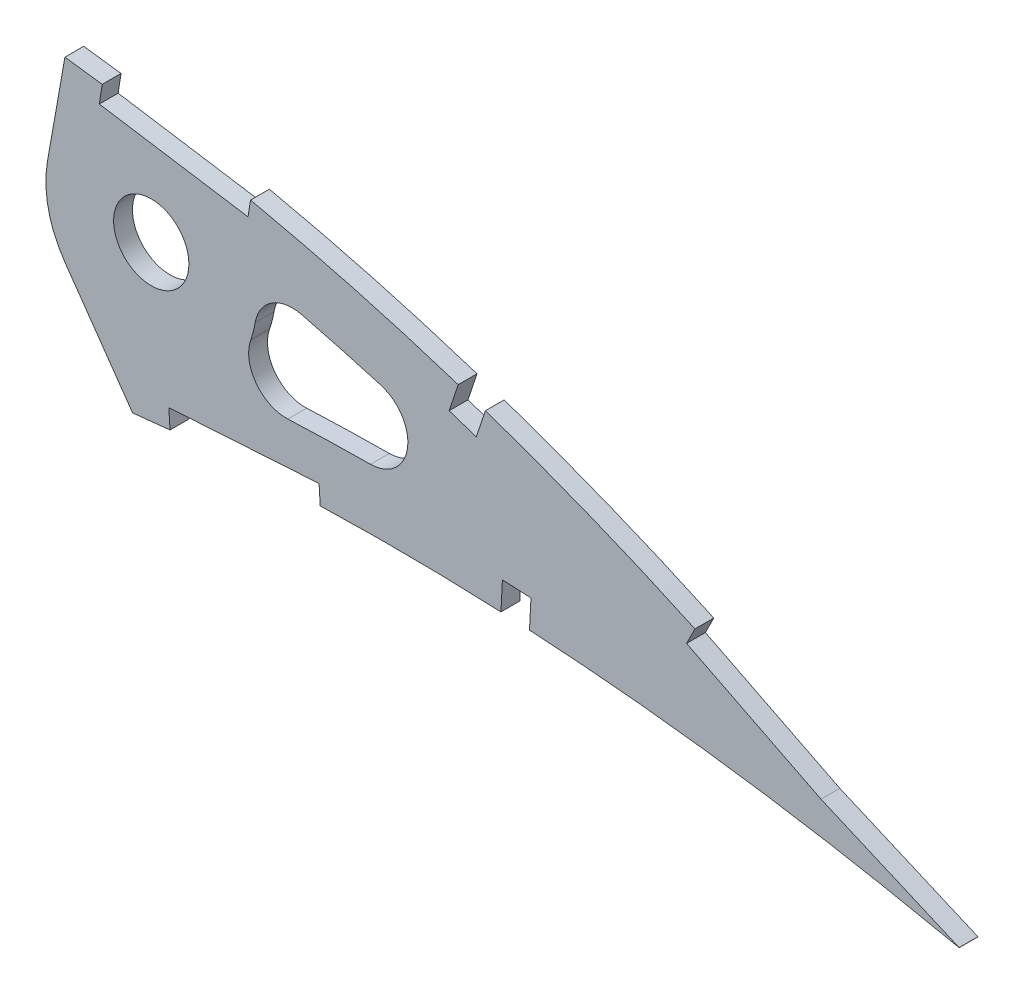
SolidWorks part; units mm, degrees
material "Plywood"
ref_plane "Front Plane" through (0, 0, 0) normal (0, 0, 1) x (1, 0, 0)
ref_plane "Top Plane" through (0, 0, 0) normal (0, 1, 0) x (1, 0, 0)
ref_plane "Right Plane" through (0, 0, 0) normal (1, 0, 0) x (0, 0, -1)
curve "Curve1"
  spline degree 3 poles (0, 0, 0) (0.1249, -0.5894, 0) (0.3751, -1.7709, 0) (1.0551, -3.4717, 0) (1.9543, -5.1067, 0) (3.0917, -6.6716, 0) (4.4597, -8.1658, 0) (6.0551, -9.5909, 0) (7.8766, -10.9463, 0) (9.9217, -12.2312, 0) (12.1874, -13.447, 0) (14.6712, -14.593, 0) (17.3708, -15.6688, 0) (20.2833, -16.6729, 0) (23.4051, -17.607, 0) (26.7332, -18.4687, 0) (30.2639, -19.2592, 0) (33.9938, -19.9766, 0) (37.9188, -20.6214, 0) (42.0348, -21.1935, 0) (46.3376, -21.6931, 0) (50.823, -22.1192, 0) (55.4866, -22.4726, 0) (60.3236, -22.7538, 0) (65.3294, -22.9634, 0) (70.4993, -23.1008, 0) (75.828, -23.1681, 0) (81.3109, -23.1662, 0) (86.9426, -23.0948, 0) (92.7182, -22.9577, 0) (98.6323, -22.754, 0) (104.6794, -22.4863, 0) (110.8541, -22.1572, 0) (117.1509, -21.7679, 0) (123.5642, -21.32, 0) (130.0885, -20.8172, 0) (136.7178, -20.2607, 0) (143.4464, -19.6538, 0) (150.2683, -18.9994, 0) (157.1776, -18.2998, 0) (164.1682, -17.5581, 0) (171.2339, -16.7767, 0) (178.3687, -15.9599, 0) (185.566, -15.1091, 0) (192.8198, -14.2292, 0) (200.1233, -13.3218, 0) (207.4703, -12.3905, 0) (214.8542, -11.4396, 0) (222.2681, -10.469, 0) (229.7058, -9.4856, 0) (237.1601, -8.4887, 0) (244.6246, -7.4833, 0) (252.0922, -6.4726, 0) (259.5558, -5.4569, 0) (267.0088, -4.4404, 0) (274.4442, -3.4259, 0) (281.8548, -2.4135, 0) (289.2339, -1.4081, 0) (296.574, -0.4098, 0) (303.8684, 0.5795, 0) (311.1101, 1.5569, 0) (318.2922, 2.521, 0) (325.4074, 3.4714, 0) (332.4485, 4.4082, 0) (339.3029, 5.3032, 0) (345.9529, 6.204, 0) (352.4207, 6.9424, 0) (358.808, 7.5727, 0) (365.1214, 8.0894, 0) (371.3533, 8.5001, 0) (377.4966, 8.8075, 0) (383.544, 9.0161, 0) (389.4878, 9.132, 0) (395.3205, 9.1582, 0) (401.0343, 9.1029, 0) (406.6218, 8.9708, 0) (412.075, 8.7675, 0) (417.3864, 8.5002, 0) (422.5485, 8.1759, 0) (427.5535, 7.7996, 0) (432.3944, 7.38, 0) (437.0637, 6.9232, 0) (441.5544, 6.4344, 0) (445.8598, 5.924, 0) (449.973, 5.3952, 0) (453.8879, 4.8568, 0) (457.5982, 4.3142, 0) (461.0979, 3.7743, 0) (464.3817, 3.2423, 0) (467.4441, 2.7253, 0) (470.2803, 2.228, 0) (472.8856, 1.7553, 0) (475.2562, 1.3133, 0) (477.3874, 0.904, 0) (479.2765, 0.5343, 0) (480.9199, 0.2058, 0) (482.3151, -0.077, 0) (483.4599, -0.3128, 0) (484.3523, -0.4979, 0) (484.9907, -0.6325, 0) (485.3743, -0.7125, 0) (485.5448, -0.7489, 0) (485.5874, -0.758, 0) knots 0 0 0 0 0.003638 0.007293 0.011028 0.014901 0.018963 0.023258 0.027821 0.032679 0.037853 0.043362 0.049215 0.055422 0.061989 0.068918 0.076211 0.083868 0.091887 0.100266 0.109 0.118085 0.127515 0.137285 0.147388 0.157816 0.168563 0.179619 0.190977 0.202627 0.21456 0.226767 0.239236 0.251959 0.264924 0.27812 0.291536 0.30516 0.318981 0.332985 0.347163 0.361499 0.375981 0.390597 0.405333 0.420175 0.43511 0.450124 0.465203 0.480333 0.495501 0.51069 0.525887 0.541078 0.556247 0.571382 0.586466 0.601485 0.616424 0.631269 0.646007 0.660621 0.675098 0.689423 0.703582 0.716908 0.730009 0.742952 0.755726 0.76832 0.780724 0.792927 0.804916 0.816679 0.828204 0.839475 0.850481 0.861208 0.871639 0.881763 0.891564 0.901027 0.910139 0.918884 0.927249 0.935221 0.942785 0.949928 0.956638 0.962904 0.968712 0.974054 0.978918 0.983297 0.98718 0.990561 0.993433 0.995791 0.99763 0.998946 0.999737 1 1 1 1
curve "Curve2"
  spline degree 3 poles (486.1938, 0.758, 0) (486.1565, 0.781, 0) (486.0077, 0.8729, 0) (485.6723, 1.0786, 0) (485.1139, 1.4213, 0) (484.3321, 1.8984, 0) (483.3276, 2.5088, 0) (482.0999, 3.2482, 0) (480.6498, 4.1141, 0) (478.9775, 5.1026, 0) (477.0833, 6.2089, 0) (474.9678, 7.4286, 0) (472.6313, 8.7548, 0) (470.0748, 10.182, 0) (467.2989, 11.7035, 0) (464.3043, 13.3123, 0) (461.0921, 15.0004, 0) (457.6635, 16.7605, 0) (454.019, 18.5827, 0) (450.1605, 20.4596, 0) (446.0892, 22.3819, 0) (441.8065, 24.3391, 0) (437.3149, 26.3234, 0) (432.6155, 28.3224, 0) (427.7112, 30.3274, 0) (422.6039, 32.3272, 0) (417.2967, 34.3124, 0) (411.7916, 36.2703, 0) (406.0928, 38.1924, 0) (400.203, 40.0661, 0) (394.1264, 41.8812, 0) (387.8666, 43.626, 0) (381.4288, 45.2916, 0) (374.8171, 46.8658, 0) (368.037, 48.3381, 0) (361.0939, 49.6996, 0) (353.9938, 50.9366, 0) (346.7562, 52.0484, 0) (339.4976, 52.9732, 0) (332.2539, 53.8802, 0) (325.021, 54.7322, 0) (317.6998, 55.5482, 0) (310.2971, 56.3235, 0) (302.8205, 57.0556, 0) (295.2774, 57.7415, 0) (287.6757, 58.3791, 0) (280.0227, 58.9648, 0) (272.3266, 59.4977, 0) (264.5949, 59.9731, 0) (256.8359, 60.3907, 0) (249.0573, 60.7475, 0) (241.2675, 61.0411, 0) (233.4745, 61.2698, 0) (225.6865, 61.4312, 0) (217.912, 61.5245, 0) (210.159, 61.547, 0) (202.4359, 61.4984, 0) (194.7508, 61.377, 0) (187.1122, 61.1811, 0) (179.5282, 60.9103, 0) (172.0069, 60.5649, 0) (164.5567, 60.1418, 0) (157.1855, 59.6438, 0) (149.9016, 59.0688, 0) (142.713, 58.4167, 0) (135.6273, 57.6901, 0) (128.6522, 56.887, 0) (121.7954, 56.0099, 0) (115.0642, 55.0603, 0) (108.4663, 54.0378, 0) (102.0087, 52.9453, 0) (95.6983, 51.784, 0) (89.542, 50.5572, 0) (83.5463, 49.2652, 0) (77.7176, 47.912, 0) (72.062, 46.4999, 0) (66.5855, 45.0315, 0) (61.2937, 43.5103, 0) (56.192, 41.9397, 0) (51.2862, 40.3215, 0) (46.5802, 38.6618, 0) (42.0796, 36.9619, 0) (37.788, 35.2268, 0) (33.7103, 33.4591, 0) (29.8497, 31.6641, 0) (26.2104, 29.8437, 0) (22.7951, 28.0033, 0) (19.6072, 26.1454, 0) (16.6497, 24.2737, 0) (13.924, 22.3929, 0) (11.4337, 20.504, 0) (9.1798, 18.612, 0) (7.1636, 16.7197, 0) (5.388, 14.8284, 0) (3.8531, 12.9414, 0) (2.5606, 11.0602, 0) (1.511, 9.1866, 0) (0.7066, 7.3219, 0) (0.1466, 5.4673, 0) (-0.16, 3.6254, 0) (-0.2363, 1.7948, 0) (-0.0786, 0.5974, 0) (0, 0, 0) knots 0 0 0 0 0.000254 0.001015 0.002283 0.004057 0.006331 0.009105 0.012374 0.016134 0.02038 0.025106 0.030306 0.035972 0.0421 0.048678 0.055702 0.06316 0.071046 0.07935 0.088063 0.097176 0.106678 0.116562 0.126814 0.137428 0.148394 0.1597 0.171338 0.183298 0.19557 0.208144 0.221012 0.234162 0.247587 0.261277 0.275223 0.289414 0.303771 0.317689 0.331784 0.34604 0.360444 0.374983 0.38964 0.404403 0.419257 0.434187 0.449177 0.464215 0.479284 0.49437 0.509458 0.524532 0.539579 0.554583 0.56953 0.584403 0.599191 0.613877 0.628447 0.642889 0.657186 0.671326 0.685294 0.699078 0.712665 0.726043 0.739198 0.752118 0.764792 0.777208 0.789356 0.801224 0.812804 0.824083 0.835055 0.84571 0.856038 0.866034 0.875689 0.884998 0.893953 0.902553 0.910789 0.918661 0.926166 0.933303 0.940071 0.946475 0.952518 0.958205 0.963547 0.968557 0.97325 0.977651 0.981787 0.985694 0.989415 0.993001 0.996508 1 1 1 1
sketch "Sketch1" plane through (0, 0, 0) normal (0, 0, 1) x (1, 0, 0)
  line L10 (485.5874, -0.758) -> (490.1477, -1.6846)
  line L24 (486.1938, 0.758) -> (490.1477, -1.6846)
  spline S2 degree 3 poles (-3866.8103, -1018.8258) (79.7559, 75.3438) (-9.1933, 22.1629) (1.0551, -3.4717) (1.9543, -5.1067) (3.0917, -6.6716) (4.4597, -8.1658) (6.0551, -9.5909) (7.8766, -10.9463) (9.9217, -12.2312) (12.1874, -13.447) (14.6712, -14.593) (17.3708, -15.6688) (20.2833, -16.6729) (23.4051, -17.607) (26.7332, -18.4687) (30.2639, -19.2592) (33.9938, -19.9766) (37.9188, -20.6214) (42.0348, -21.1935) (46.3376, -21.6931) (50.823, -22.1192) (55.4866, -22.4726) (60.3236, -22.7538) (65.3294, -22.9634) (70.4993, -23.1008) (75.828, -23.1681) (81.3109, -23.1662) (86.9426, -23.0948) (92.7182, -22.9577) (98.6323, -22.754) (104.6794, -22.4863) (110.8541, -22.1572) (117.1509, -21.7679) (123.5642, -21.32) (130.0885, -20.8172) (136.7178, -20.2607) (143.4464, -19.6538) (150.2683, -18.9994) (157.1776, -18.2998) (164.1682, -17.5581) (171.2339, -16.7767) (178.3687, -15.9599) (185.566, -15.1091) (192.8198, -14.2292) (200.1233, -13.3218) (207.4703, -12.3905) (214.8542, -11.4396) (222.2681, -10.469) (229.7058, -9.4856) (237.1601, -8.4887) (244.6246, -7.4833) (252.0922, -6.4726) (259.5558, -5.4569) (267.0088, -4.4404) (274.4442, -3.4259) (281.8548, -2.4135) (289.2339, -1.4081) (296.574, -0.4098) (303.8684, 0.5795) (311.1101, 1.5569) (318.2922, 2.521) (325.4074, 3.4714) (332.4485, 4.4082) (339.3029, 5.3032) (345.9529, 6.204) (352.4207, 6.9424) (358.808, 7.5727) (365.1214, 8.0894) (371.3533, 8.5001) (377.4966, 8.8075) (383.544, 9.0161) (389.4878, 9.132) (395.3205, 9.1582) (401.0343, 9.1029) (406.6218, 8.9708) (412.075, 8.7675) (417.3864, 8.5002) (422.5485, 8.1759) (427.5535, 7.7996) (432.3944, 7.38) (437.0637, 6.9232) (441.5544, 6.4344) (445.8598, 5.924) (449.973, 5.3952) (453.8879, 4.8568) (457.5982, 4.3142) (461.0979, 3.7743) (464.3817, 3.2423) (467.4441, 2.7253) (470.2803, 2.228) (472.8856, 1.7553) (475.2562, 1.3133) (477.3874, 0.904) (479.2765, 0.5343) (480.9199, 0.2058) (482.3151, -0.077) (483.4599, -0.3128) (484.3523, -0.4979) (484.9907, -0.6325) (504.0158, -4.6034) (520.901, -17.6411) (1368.8084, 3899.3631) knots -0.155184 -0.155184 -0.155184 -0.155184 0.003638 0.007293 0.011028 0.014901 0.018963 0.023258 0.027821 0.032679 0.037853 0.043362 0.049215 0.055422 0.061989 0.068918 0.076211 0.083868 0.091887 0.100266 0.109 0.118085 0.127515 0.137285 0.147388 0.157816 0.168563 0.179619 0.190977 0.202627 0.21456 0.226767 0.239236 0.251959 0.264924 0.27812 0.291536 0.30516 0.318981 0.332985 0.347163 0.361499 0.375981 0.390597 0.405333 0.420175 0.43511 0.450124 0.465203 0.480333 0.495501 0.51069 0.525887 0.541078 0.556247 0.571382 0.586466 0.601485 0.616424 0.631269 0.646007 0.660621 0.675098 0.689423 0.703582 0.716908 0.730009 0.742952 0.755726 0.76832 0.780724 0.792927 0.804916 0.816679 0.828204 0.839475 0.850481 0.861208 0.871639 0.881763 0.891564 0.901027 0.910139 0.918884 0.927249 0.935221 0.942785 0.949928 0.956638 0.962904 0.968712 0.974054 0.978918 0.983297 0.98718 0.990561 0.993433 0.995791 0.99763 0.998946 0.999737 1.115177 1.115177 1.115177 1.115177 only from (0, 0) to (485.5874, -0.758) construction
  spline S3 degree 3 poles (2637.6242, 3371.1949) (518.0891, -28.6046) (504.1645, -10.2642) (485.6723, 1.0786) (485.1139, 1.4213) (484.3321, 1.8984) (483.3276, 2.5088) (482.0999, 3.2482) (480.6498, 4.1141) (478.9775, 5.1026) (477.0833, 6.2089) (474.9678, 7.4286) (472.6313, 8.7548) (470.0748, 10.182) (467.2989, 11.7035) (464.3043, 13.3123) (461.0921, 15.0004) (457.6635, 16.7605) (454.019, 18.5827) (450.1605, 20.4596) (446.0892, 22.3819) (441.8065, 24.3391) (437.3149, 26.3234) (432.6155, 28.3224) (427.7112, 30.3274) (422.6039, 32.3272) (417.2967, 34.3124) (411.7916, 36.2703) (406.0928, 38.1924) (400.203, 40.0661) (394.1264, 41.8812) (387.8666, 43.626) (381.4288, 45.2916) (374.8171, 46.8658) (368.037, 48.3381) (361.0939, 49.6996) (353.9938, 50.9366) (346.7562, 52.0484) (339.4976, 52.9732) (332.2539, 53.8802) (325.021, 54.7322) (317.6998, 55.5482) (310.2971, 56.3235) (302.8205, 57.0556) (295.2774, 57.7415) (287.6757, 58.3791) (280.0227, 58.9648) (272.3266, 59.4977) (264.5949, 59.9731) (256.8359, 60.3907) (249.0573, 60.7475) (241.2675, 61.0411) (233.4745, 61.2698) (225.6865, 61.4312) (217.912, 61.5245) (210.159, 61.547) (202.4359, 61.4984) (194.7508, 61.377) (187.1122, 61.1811) (179.5282, 60.9103) (172.0069, 60.5649) (164.5567, 60.1418) (157.1855, 59.6438) (149.9016, 59.0688) (142.713, 58.4167) (135.6273, 57.6901) (128.6522, 56.887) (121.7954, 56.0099) (115.0642, 55.0603) (108.4663, 54.0378) (102.0087, 52.9453) (95.6983, 51.784) (89.542, 50.5572) (83.5463, 49.2652) (77.7176, 47.912) (72.062, 46.4999) (66.5855, 45.0315) (61.2937, 43.5103) (56.192, 41.9397) (51.2862, 40.3215) (46.5802, 38.6618) (42.0796, 36.9619) (37.788, 35.2268) (33.7103, 33.4591) (29.8497, 31.6641) (26.2104, 29.8437) (22.7951, 28.0033) (19.6072, 26.1454) (16.6497, 24.2737) (13.924, 22.3929) (11.4337, 20.504) (9.1798, 18.612) (7.1636, 16.7197) (5.388, 14.8284) (3.8531, 12.9414) (2.5606, 11.0602) (1.511, 9.1866) (0.7066, 7.3219) (0.1466, 5.4673) (-0.16, 3.6254) (-1.3078, -23.9112) (100.477, -44.4073) (-3985.5392, -325.5751) knots -0.123624 -0.123624 -0.123624 -0.123624 0.000254 0.001015 0.002283 0.004057 0.006331 0.009105 0.012374 0.016134 0.02038 0.025106 0.030306 0.035972 0.0421 0.048678 0.055702 0.06316 0.071046 0.07935 0.088063 0.097176 0.106678 0.116562 0.126814 0.137428 0.148394 0.1597 0.171338 0.183298 0.19557 0.208144 0.221012 0.234162 0.247587 0.261277 0.275223 0.289414 0.303771 0.317689 0.331784 0.34604 0.360444 0.374983 0.38964 0.404403 0.419257 0.434187 0.449177 0.464215 0.479284 0.49437 0.509458 0.524532 0.539579 0.554583 0.56953 0.584403 0.599191 0.613877 0.628447 0.642889 0.657186 0.671326 0.685294 0.699078 0.712665 0.726043 0.739198 0.752118 0.764792 0.777208 0.789356 0.801224 0.812804 0.824083 0.835055 0.84571 0.856038 0.866034 0.875689 0.884998 0.893953 0.902553 0.910789 0.918661 0.926166 0.933303 0.940071 0.946475 0.952518 0.958205 0.963547 0.968557 0.97325 0.977651 0.981787 0.985694 0.989415 0.993001 0.996508 1.148636 1.148636 1.148636 1.148636 only from (486.1938, 0.758) to (0, 0) construction
  spline S4 degree 3 poles (0, 0) (0.1249, -0.5894) (0.3751, -1.7709) (1.0551, -3.4717) (1.9543, -5.1067) (3.0917, -6.6716) (4.4597, -8.1658) (6.0551, -9.5909) (7.8766, -10.9463) (9.9217, -12.2312) (12.1874, -13.447) (14.6712, -14.593) (17.3708, -15.6688) (20.2833, -16.6729) (23.4051, -17.607) (26.7332, -18.4687) (30.2639, -19.2592) (33.9938, -19.9766) (37.9188, -20.6214) (42.0348, -21.1935) (46.3376, -21.6931) (50.823, -22.1192) (55.4866, -22.4726) (60.3236, -22.7538) (65.3294, -22.9634) (70.4993, -23.1008) (75.828, -23.1681) (81.3109, -23.1662) (86.9426, -23.0948) (92.7182, -22.9577) (98.6323, -22.754) (104.6794, -22.4863) (110.8541, -22.1572) (117.1509, -21.7679) (123.5642, -21.32) (130.0885, -20.8172) (136.7178, -20.2607) (143.4464, -19.6538) (150.2683, -18.9994) (157.1776, -18.2998) (164.1682, -17.5581) (171.2339, -16.7767) (178.3687, -15.9599) (185.566, -15.1091) (192.8198, -14.2292) (200.1233, -13.3218) (207.4703, -12.3905) (214.8542, -11.4396) (222.2681, -10.469) (229.7058, -9.4856) (237.1601, -8.4887) (244.6246, -7.4833) (252.0922, -6.4726) (259.5558, -5.4569) (267.0088, -4.4404) (274.4442, -3.4259) (281.8548, -2.4135) (289.2339, -1.4081) (296.574, -0.4098) (303.8684, 0.5795) (311.1101, 1.5569) (318.2922, 2.521) (325.4074, 3.4714) (332.4485, 4.4082) (339.3029, 5.3032) (345.9529, 6.204) (352.4207, 6.9424) (358.808, 7.5727) (365.1214, 8.0894) (371.3533, 8.5001) (377.4966, 8.8075) (383.544, 9.0161) (389.4878, 9.132) (395.3205, 9.1582) (401.0343, 9.1029) (406.6218, 8.9708) (412.075, 8.7675) (417.3864, 8.5002) (422.5485, 8.1759) (427.5535, 7.7996) (432.3944, 7.38) (437.0637, 6.9232) (441.5544, 6.4344) (445.8598, 5.924) (449.973, 5.3952) (453.8879, 4.8568) (457.5982, 4.3142) (461.0979, 3.7743) (464.3817, 3.2423) (467.4441, 2.7253) (470.2803, 2.228) (472.8856, 1.7553) (475.2562, 1.3133) (477.3874, 0.904) (479.2765, 0.5343) (480.9199, 0.2058) (482.3151, -0.077) (483.4599, -0.3128) (484.3523, -0.4979) (484.9907, -0.6325) (485.3743, -0.7125) (485.5448, -0.7489) (485.5874, -0.758) knots 0 0 0 0 0.003638 0.007293 0.011028 0.014901 0.018963 0.023258 0.027821 0.032679 0.037853 0.043362 0.049215 0.055422 0.061989 0.068918 0.076211 0.083868 0.091887 0.100266 0.109 0.118085 0.127515 0.137285 0.147388 0.157816 0.168563 0.179619 0.190977 0.202627 0.21456 0.226767 0.239236 0.251959 0.264924 0.27812 0.291536 0.30516 0.318981 0.332985 0.347163 0.361499 0.375981 0.390597 0.405333 0.420175 0.43511 0.450124 0.465203 0.480333 0.495501 0.51069 0.525887 0.541078 0.556247 0.571382 0.586466 0.601485 0.616424 0.631269 0.646007 0.660621 0.675098 0.689423 0.703582 0.716908 0.730009 0.742952 0.755726 0.76832 0.780724 0.792927 0.804916 0.816679 0.828204 0.839475 0.850481 0.861208 0.871639 0.881763 0.891564 0.901027 0.910139 0.918884 0.927249 0.935221 0.942785 0.949928 0.956638 0.962904 0.968712 0.974054 0.978918 0.983297 0.98718 0.990561 0.993433 0.995791 0.99763 0.998946 0.999737 1 1 1 1
  spline S5 degree 3 poles (486.1938, 0.758) (486.1565, 0.781) (486.0077, 0.8729) (485.6723, 1.0786) (485.1139, 1.4213) (484.3321, 1.8984) (483.3276, 2.5088) (482.0999, 3.2482) (480.6498, 4.1141) (478.9775, 5.1026) (477.0833, 6.2089) (474.9678, 7.4286) (472.6313, 8.7548) (470.0748, 10.182) (467.2989, 11.7035) (464.3043, 13.3123) (461.0921, 15.0004) (457.6635, 16.7605) (454.019, 18.5827) (450.1605, 20.4596) (446.0892, 22.3819) (441.8065, 24.3391) (437.3149, 26.3234) (432.6155, 28.3224) (427.7112, 30.3274) (422.6039, 32.3272) (417.2967, 34.3124) (411.7916, 36.2703) (406.0928, 38.1924) (400.203, 40.0661) (394.1264, 41.8812) (387.8666, 43.626) (381.4288, 45.2916) (374.8171, 46.8658) (368.037, 48.3381) (361.0939, 49.6996) (353.9938, 50.9366) (346.7562, 52.0484) (339.4976, 52.9732) (332.2539, 53.8802) (325.021, 54.7322) (317.6998, 55.5482) (310.2971, 56.3235) (302.8205, 57.0556) (295.2774, 57.7415) (287.6757, 58.3791) (280.0227, 58.9648) (272.3266, 59.4977) (264.5949, 59.9731) (256.8359, 60.3907) (249.0573, 60.7475) (241.2675, 61.0411) (233.4745, 61.2698) (225.6865, 61.4312) (217.912, 61.5245) (210.159, 61.547) (202.4359, 61.4984) (194.7508, 61.377) (187.1122, 61.1811) (179.5282, 60.9103) (172.0069, 60.5649) (164.5567, 60.1418) (157.1855, 59.6438) (149.9016, 59.0688) (142.713, 58.4167) (135.6273, 57.6901) (128.6522, 56.887) (121.7954, 56.0099) (115.0642, 55.0603) (108.4663, 54.0378) (102.0087, 52.9453) (95.6983, 51.784) (89.542, 50.5572) (83.5463, 49.2652) (77.7176, 47.912) (72.062, 46.4999) (66.5855, 45.0315) (61.2937, 43.5103) (56.192, 41.9397) (51.2862, 40.3215) (46.5802, 38.6618) (42.0796, 36.9619) (37.788, 35.2268) (33.7103, 33.4591) (29.8497, 31.6641) (26.2104, 29.8437) (22.7951, 28.0033) (19.6072, 26.1454) (16.6497, 24.2737) (13.924, 22.3929) (11.4337, 20.504) (9.1798, 18.612) (7.1636, 16.7197) (5.388, 14.8284) (3.8531, 12.9414) (2.5606, 11.0602) (1.511, 9.1866) (0.7066, 7.3219) (0.1466, 5.4673) (-0.16, 3.6254) (-0.2363, 1.7948) (-0.0786, 0.5974) (0, 0) knots 0 0 0 0 0.000254 0.001015 0.002283 0.004057 0.006331 0.009105 0.012374 0.016134 0.02038 0.025106 0.030306 0.035972 0.0421 0.048678 0.055702 0.06316 0.071046 0.07935 0.088063 0.097176 0.106678 0.116562 0.126814 0.137428 0.148394 0.1597 0.171338 0.183298 0.19557 0.208144 0.221012 0.234162 0.247587 0.261277 0.275223 0.289414 0.303771 0.317689 0.331784 0.34604 0.360444 0.374983 0.38964 0.404403 0.419257 0.434187 0.449177 0.464215 0.479284 0.49437 0.509458 0.524532 0.539579 0.554583 0.56953 0.584403 0.599191 0.613877 0.628447 0.642889 0.657186 0.671326 0.685294 0.699078 0.712665 0.726043 0.739198 0.752118 0.764792 0.777208 0.789356 0.801224 0.812804 0.824083 0.835055 0.84571 0.856038 0.866034 0.875689 0.884998 0.893953 0.902553 0.910789 0.918661 0.926166 0.933303 0.940071 0.946475 0.952518 0.958205 0.963547 0.968557 0.97325 0.977651 0.981787 0.985694 0.989415 0.993001 0.996508 1 1 1 1
extrude "Boss-Extrude1" add sketch "Sketch1" along normal blind 3.175
sketch "Sketch5" plane through (0, 0, 3.175) normal (0, 0, 1) x (1, 0, 0)
  line L0 (336.323, 36.32) -> (339.2642, 53)
  line L1 (339.2684, 23.0344) -> (350.6801, 6.7368)
  line L2 (353.8329, 33.2326) -> (374.466, 33.2326)
  circle A0 centre (353.8329, 33.2326) radius 6.35
  circle A1 centre (353.8329, 33.2326) radius 6.35
  circle A2 centre (353.8329, 33.2326) radius 17.78
  spline S0 degree 3 poles (-1939.0794, -487.5307) (48.5631, 55.4905) (-7.2206, 17.2286) (1.0551, -3.4717) (1.9543, -5.1067) (3.0917, -6.6716) (4.4597, -8.1658) (6.0551, -9.5909) (7.8766, -10.9463) (9.9217, -12.2312) (12.1874, -13.447) (14.6712, -14.593) (17.3708, -15.6688) (20.2833, -16.6729) (23.4051, -17.607) (26.7332, -18.4687) (30.2639, -19.2592) (33.9938, -19.9766) (37.9188, -20.6214) (42.0348, -21.1935) (46.3376, -21.6931) (50.823, -22.1192) (55.4866, -22.4726) (60.3236, -22.7538) (65.3294, -22.9634) (70.4993, -23.1008) (75.828, -23.1681) (81.3109, -23.1662) (86.9426, -23.0948) (92.7182, -22.9577) (98.6323, -22.754) (104.6794, -22.4863) (110.8541, -22.1572) (117.1509, -21.7679) (123.5642, -21.32) (130.0885, -20.8172) (136.7178, -20.2607) (143.4464, -19.6538) (150.2683, -18.9994) (157.1776, -18.2998) (164.1682, -17.5581) (171.2339, -16.7767) (178.3687, -15.9599) (185.566, -15.1091) (192.8198, -14.2292) (200.1233, -13.3218) (207.4703, -12.3905) (214.8542, -11.4396) (222.2681, -10.469) (229.7058, -9.4856) (237.1601, -8.4887) (244.6246, -7.4833) (252.0922, -6.4726) (259.5558, -5.4569) (267.0088, -4.4404) (274.4442, -3.4259) (281.8548, -2.4135) (289.2339, -1.4081) (296.574, -0.4098) (303.8684, 0.5795) (311.1101, 1.5569) (318.2922, 2.521) (325.4074, 3.4714) (332.4485, 4.4082) (339.3029, 5.3032) (345.9529, 6.204) (352.4207, 6.9424) (358.808, 7.5727) (365.1214, 8.0894) (371.3533, 8.5001) (377.4966, 8.8075) (383.544, 9.0161) (389.4878, 9.132) (395.3205, 9.1582) (401.0343, 9.1029) (406.6218, 8.9708) (412.075, 8.7675) (417.3864, 8.5002) (422.5485, 8.1759) (427.5535, 7.7996) (432.3944, 7.38) (437.0637, 6.9232) (441.5544, 6.4344) (445.8598, 5.924) (449.973, 5.3952) (453.8879, 4.8568) (457.5982, 4.3142) (461.0979, 3.7743) (464.3817, 3.2423) (467.4441, 2.7253) (470.2803, 2.228) (472.8856, 1.7553) (475.2562, 1.3133) (477.3874, 0.904) (479.2765, 0.5343) (480.9199, 0.2058) (482.3151, -0.077) (483.4599, -0.3128) (484.3523, -0.4979) (484.9907, -0.6325) (500.1693, -3.8005) (513.9154, -12.6904) (943.5402, 1945.4943) knots -0.123191 -0.123191 -0.123191 -0.123191 0.003638 0.007293 0.011028 0.014901 0.018963 0.023258 0.027821 0.032679 0.037853 0.043362 0.049215 0.055422 0.061989 0.068918 0.076211 0.083868 0.091887 0.100266 0.109 0.118085 0.127515 0.137285 0.147388 0.157816 0.168563 0.179619 0.190977 0.202627 0.21456 0.226767 0.239236 0.251959 0.264924 0.27812 0.291536 0.30516 0.318981 0.332985 0.347163 0.361499 0.375981 0.390597 0.405333 0.420175 0.43511 0.450124 0.465203 0.480333 0.495501 0.51069 0.525887 0.541078 0.556247 0.571382 0.586466 0.601485 0.616424 0.631269 0.646007 0.660621 0.675098 0.689423 0.703582 0.716908 0.730009 0.742952 0.755726 0.76832 0.780724 0.792927 0.804916 0.816679 0.828204 0.839475 0.850481 0.861208 0.871639 0.881763 0.891564 0.901027 0.910139 0.918884 0.927249 0.935221 0.942785 0.949928 0.956638 0.962904 0.968712 0.974054 0.978918 0.983297 0.98718 0.990561 0.993433 0.995791 0.99763 0.998946 0.999737 1.091411 1.091411 1.091411 1.091411 only from (0, 0) to (485.5874, -0.758) construction
  spline S1 degree 3 poles (1577.8242, 1676.0308) (512.2068, -21.3963) (500.4185, -7.9664) (485.6723, 1.0786) (485.1139, 1.4213) (484.3321, 1.8984) (483.3276, 2.5088) (482.0999, 3.2482) (480.6498, 4.1141) (478.9775, 5.1026) (477.0833, 6.2089) (474.9678, 7.4286) (472.6313, 8.7548) (470.0748, 10.182) (467.2989, 11.7035) (464.3043, 13.3123) (461.0921, 15.0004) (457.6635, 16.7605) (454.019, 18.5827) (450.1605, 20.4596) (446.0892, 22.3819) (441.8065, 24.3391) (437.3149, 26.3234) (432.6155, 28.3224) (427.7112, 30.3274) (422.6039, 32.3272) (417.2967, 34.3124) (411.7916, 36.2703) (406.0928, 38.1924) (400.203, 40.0661) (394.1264, 41.8812) (387.8666, 43.626) (381.4288, 45.2916) (374.8171, 46.8658) (368.037, 48.3381) (361.0939, 49.6996) (353.9938, 50.9366) (346.7562, 52.0484) (339.4976, 52.9732) (332.2539, 53.8802) (325.021, 54.7322) (317.6998, 55.5482) (310.2971, 56.3235) (302.8205, 57.0556) (295.2774, 57.7415) (287.6757, 58.3791) (280.0227, 58.9648) (272.3266, 59.4977) (264.5949, 59.9731) (256.8359, 60.3907) (249.0573, 60.7475) (241.2675, 61.0411) (233.4745, 61.2698) (225.6865, 61.4312) (217.912, 61.5245) (210.159, 61.547) (202.4359, 61.4984) (194.7508, 61.377) (187.1122, 61.1811) (179.5282, 60.9103) (172.0069, 60.5649) (164.5567, 60.1418) (157.1855, 59.6438) (149.9016, 59.0688) (142.713, 58.4167) (135.6273, 57.6901) (128.6522, 56.887) (121.7954, 56.0099) (115.0642, 55.0603) (108.4663, 54.0378) (102.0087, 52.9453) (95.6983, 51.784) (89.542, 50.5572) (83.5463, 49.2652) (77.7176, 47.912) (72.062, 46.4999) (66.5855, 45.0315) (61.2937, 43.5103) (56.192, 41.9397) (51.2862, 40.3215) (46.5802, 38.6618) (42.0796, 36.9619) (37.788, 35.2268) (33.7103, 33.4591) (29.8497, 31.6641) (26.2104, 29.8437) (22.7951, 28.0033) (19.6072, 26.1454) (16.6497, 24.2737) (13.924, 22.3929) (11.4337, 20.504) (9.1798, 18.612) (7.1636, 16.7197) (5.388, 14.8284) (3.8531, 12.9414) (2.5606, 11.0602) (1.511, 9.1866) (0.7066, 7.3219) (0.1466, 5.4673) (-0.16, 3.6254) (-1.0869, -18.6116) (64.385, -36.0874) (-1990.8444, -185.2686) knots -0.098119 -0.098119 -0.098119 -0.098119 0.000254 0.001015 0.002283 0.004057 0.006331 0.009105 0.012374 0.016134 0.02038 0.025106 0.030306 0.035972 0.0421 0.048678 0.055702 0.06316 0.071046 0.07935 0.088063 0.097176 0.106678 0.116562 0.126814 0.137428 0.148394 0.1597 0.171338 0.183298 0.19557 0.208144 0.221012 0.234162 0.247587 0.261277 0.275223 0.289414 0.303771 0.317689 0.331784 0.34604 0.360444 0.374983 0.38964 0.404403 0.419257 0.434187 0.449177 0.464215 0.479284 0.49437 0.509458 0.524532 0.539579 0.554583 0.56953 0.584403 0.599191 0.613877 0.628447 0.642889 0.657186 0.671326 0.685294 0.699078 0.712665 0.726043 0.739198 0.752118 0.764792 0.777208 0.789356 0.801224 0.812804 0.824083 0.835055 0.84571 0.856038 0.866034 0.875689 0.884998 0.893953 0.902553 0.910789 0.918661 0.926166 0.933303 0.940071 0.946475 0.952518 0.958205 0.963547 0.968557 0.97325 0.977651 0.981787 0.985694 0.989415 0.993001 0.996508 1.117993 1.117993 1.117993 1.117993 only from (486.1938, 0.758) to (0, 0) construction
  spline S2 degree 3 poles (0, 0) (0.1249, -0.5894) (0.3751, -1.7709) (1.0551, -3.4717) (1.9543, -5.1067) (3.0917, -6.6716) (4.4597, -8.1658) (6.0551, -9.5909) (7.8766, -10.9463) (9.9217, -12.2312) (12.1874, -13.447) (14.6712, -14.593) (17.3708, -15.6688) (20.2833, -16.6729) (23.4051, -17.607) (26.7332, -18.4687) (30.2639, -19.2592) (33.9938, -19.9766) (37.9188, -20.6214) (42.0348, -21.1935) (46.3376, -21.6931) (50.823, -22.1192) (55.4866, -22.4726) (60.3236, -22.7538) (65.3294, -22.9634) (70.4993, -23.1008) (75.828, -23.1681) (81.3109, -23.1662) (86.9426, -23.0948) (92.7182, -22.9577) (98.6323, -22.754) (104.6794, -22.4863) (110.8541, -22.1572) (117.1509, -21.7679) (123.5642, -21.32) (130.0885, -20.8172) (136.7178, -20.2607) (143.4464, -19.6538) (150.2683, -18.9994) (157.1776, -18.2998) (164.1682, -17.5581) (171.2339, -16.7767) (178.3687, -15.9599) (185.566, -15.1091) (192.8198, -14.2292) (200.1233, -13.3218) (207.4703, -12.3905) (214.8542, -11.4396) (222.2681, -10.469) (229.7058, -9.4856) (237.1601, -8.4887) (244.6246, -7.4833) (252.0922, -6.4726) (259.5558, -5.4569) (267.0088, -4.4404) (274.4442, -3.4259) (281.8548, -2.4135) (289.2339, -1.4081) (296.574, -0.4098) (303.8684, 0.5795) (311.1101, 1.5569) (318.2922, 2.521) (325.4074, 3.4714) (332.4485, 4.4082) (339.3029, 5.3032) (345.9529, 6.204) (352.4207, 6.9424) (358.808, 7.5727) (365.1214, 8.0894) (371.3533, 8.5001) (377.4966, 8.8075) (383.544, 9.0161) (389.4878, 9.132) (395.3205, 9.1582) (401.0343, 9.1029) (406.6218, 8.9708) (412.075, 8.7675) (417.3864, 8.5002) (422.5485, 8.1759) (427.5535, 7.7996) (432.3944, 7.38) (437.0637, 6.9232) (441.5544, 6.4344) (445.8598, 5.924) (449.973, 5.3952) (453.8879, 4.8568) (457.5982, 4.3142) (461.0979, 3.7743) (464.3817, 3.2423) (467.4441, 2.7253) (470.2803, 2.228) (472.8856, 1.7553) (475.2562, 1.3133) (477.3874, 0.904) (479.2765, 0.5343) (480.9199, 0.2058) (482.3151, -0.077) (483.4599, -0.3128) (484.3523, -0.4979) (484.9907, -0.6325) (485.3743, -0.7125) (485.5448, -0.7489) (485.5874, -0.758) knots 0 0 0 0 0.003638 0.007293 0.011028 0.014901 0.018963 0.023258 0.027821 0.032679 0.037853 0.043362 0.049215 0.055422 0.061989 0.068918 0.076211 0.083868 0.091887 0.100266 0.109 0.118085 0.127515 0.137285 0.147388 0.157816 0.168563 0.179619 0.190977 0.202627 0.21456 0.226767 0.239236 0.251959 0.264924 0.27812 0.291536 0.30516 0.318981 0.332985 0.347163 0.361499 0.375981 0.390597 0.405333 0.420175 0.43511 0.450124 0.465203 0.480333 0.495501 0.51069 0.525887 0.541078 0.556247 0.571382 0.586466 0.601485 0.616424 0.631269 0.646007 0.660621 0.675098 0.689423 0.703582 0.716908 0.730009 0.742952 0.755726 0.76832 0.780724 0.792927 0.804916 0.816679 0.828204 0.839475 0.850481 0.861208 0.871639 0.881763 0.891564 0.901027 0.910139 0.918884 0.927249 0.935221 0.942785 0.949928 0.956638 0.962904 0.968712 0.974054 0.978918 0.983297 0.98718 0.990561 0.993433 0.995791 0.99763 0.998946 0.999737 1 1 1 1
  spline S3 degree 3 poles (486.1938, 0.758) (486.1565, 0.781) (486.0077, 0.8729) (485.6723, 1.0786) (485.1139, 1.4213) (484.3321, 1.8984) (483.3276, 2.5088) (482.0999, 3.2482) (480.6498, 4.1141) (478.9775, 5.1026) (477.0833, 6.2089) (474.9678, 7.4286) (472.6313, 8.7548) (470.0748, 10.182) (467.2989, 11.7035) (464.3043, 13.3123) (461.0921, 15.0004) (457.6635, 16.7605) (454.019, 18.5827) (450.1605, 20.4596) (446.0892, 22.3819) (441.8065, 24.3391) (437.3149, 26.3234) (432.6155, 28.3224) (427.7112, 30.3274) (422.6039, 32.3272) (417.2967, 34.3124) (411.7916, 36.2703) (406.0928, 38.1924) (400.203, 40.0661) (394.1264, 41.8812) (387.8666, 43.626) (381.4288, 45.2916) (374.8171, 46.8658) (368.037, 48.3381) (361.0939, 49.6996) (353.9938, 50.9366) (346.7562, 52.0484) (339.4976, 52.9732) (332.2539, 53.8802) (325.021, 54.7322) (317.6998, 55.5482) (310.2971, 56.3235) (302.8205, 57.0556) (295.2774, 57.7415) (287.6757, 58.3791) (280.0227, 58.9648) (272.3266, 59.4977) (264.5949, 59.9731) (256.8359, 60.3907) (249.0573, 60.7475) (241.2675, 61.0411) (233.4745, 61.2698) (225.6865, 61.4312) (217.912, 61.5245) (210.159, 61.547) (202.4359, 61.4984) (194.7508, 61.377) (187.1122, 61.1811) (179.5282, 60.9103) (172.0069, 60.5649) (164.5567, 60.1418) (157.1855, 59.6438) (149.9016, 59.0688) (142.713, 58.4167) (135.6273, 57.6901) (128.6522, 56.887) (121.7954, 56.0099) (115.0642, 55.0603) (108.4663, 54.0378) (102.0087, 52.9453) (95.6983, 51.784) (89.542, 50.5572) (83.5463, 49.2652) (77.7176, 47.912) (72.062, 46.4999) (66.5855, 45.0315) (61.2937, 43.5103) (56.192, 41.9397) (51.2862, 40.3215) (46.5802, 38.6618) (42.0796, 36.9619) (37.788, 35.2268) (33.7103, 33.4591) (29.8497, 31.6641) (26.2104, 29.8437) (22.7951, 28.0033) (19.6072, 26.1454) (16.6497, 24.2737) (13.924, 22.3929) (11.4337, 20.504) (9.1798, 18.612) (7.1636, 16.7197) (5.388, 14.8284) (3.8531, 12.9414) (2.5606, 11.0602) (1.511, 9.1866) (0.7066, 7.3219) (0.1466, 5.4673) (-0.16, 3.6254) (-0.2363, 1.7948) (-0.0786, 0.5974) (0, 0) knots 0 0 0 0 0.000254 0.001015 0.002283 0.004057 0.006331 0.009105 0.012374 0.016134 0.02038 0.025106 0.030306 0.035972 0.0421 0.048678 0.055702 0.06316 0.071046 0.07935 0.088063 0.097176 0.106678 0.116562 0.126814 0.137428 0.148394 0.1597 0.171338 0.183298 0.19557 0.208144 0.221012 0.234162 0.247587 0.261277 0.275223 0.289414 0.303771 0.317689 0.331784 0.34604 0.360444 0.374983 0.38964 0.404403 0.419257 0.434187 0.449177 0.464215 0.479284 0.49437 0.509458 0.524532 0.539579 0.554583 0.56953 0.584403 0.599191 0.613877 0.628447 0.642889 0.657186 0.671326 0.685294 0.699078 0.712665 0.726043 0.739198 0.752118 0.764792 0.777208 0.789356 0.801224 0.812804 0.824083 0.835055 0.84571 0.856038 0.866034 0.875689 0.884998 0.893953 0.902553 0.910789 0.918661 0.926166 0.933303 0.940071 0.946475 0.952518 0.958205 0.963547 0.968557 0.97325 0.977651 0.981787 0.985694 0.989415 0.993001 0.996508 1 1 1 1
  spline S4 degree 1 poles (480.8541, -7.8857) (10.0221, 1.7185) knots 0 0 1 1 construction
  spline S5 degree 1 poles (10.0221, 1.7185) (487.707, 9.1785) knots 0 0 1 1 construction
  spline S6 degree 3 poles (480.8541, -7.8857) (480.7201, -7.8029) (480.4589, -7.6425) (479.8783, -7.2863) (478.9124, -6.6962) (476.9448, -5.5034) (473.0052, -3.1584) (465.0526, 1.417) (448.8811, 10.0668) (425.053, 20.9312) (400.3824, 29.6362) (380.244, 35.2169) (367.5068, 38.1191) (357.2621, 40.0741) (349.5101, 41.3746) (341.8335, 42.449) (333.8166, 43.4475) (325.9049, 44.4061) (315.2983, 45.6009) (296.7451, 47.4959) (270.1814, 49.6136) (238.2719, 51.1465) (206.364, 51.5674) (174.5136, 50.7436) (142.8023, 48.4874) (116.597, 45.208) (95.874, 41.5554) (80.5049, 38.2363) (65.3742, 34.2512) (53.0577, 30.2789) (43.4884, 26.6248) (36.4997, 23.6156) (29.7711, 20.3046) (23.4201, 16.6518) (17.6543, 12.6276) (13.6768, 8.9843) (11.4208, 6.112) (10.5313, 4.5112) (10.1421, 3.4379) (10.0302, 2.9559) (9.9731, 2.5067) (9.9642, 2.3114) (9.9656, 2.2504) (9.9657, 2.2359) (9.9791, 2.0811) (9.9996, 1.9002) (10.0148, 1.7763) (10.0221, 1.7185) knots 0 0 0 0 0.000976 0.001951 0.003903 0.007806 0.015611 0.031223 0.062446 0.124891 0.187337 0.21856 0.249783 0.265394 0.281006 0.296617 0.312229 0.32784 0.343451 0.374674 0.43712 0.499566 0.562011 0.624457 0.686903 0.749348 0.780571 0.811794 0.843017 0.87424 0.889851 0.905463 0.921074 0.936686 0.952297 0.967908 0.975714 0.98352 0.987423 0.991326 0.993277 0.995228 0.996204 0.99718 0.998156 0.998643 0.999131 0.999131 0.999131 0.999131
  spline S7 degree 3 poles (10.0221, 1.7185) (10.034, 1.6636) (10.0599, 1.5462) (10.0999, 1.3723) (10.1389, 1.2199) (10.1476, 1.1921) (10.1628, 1.1452) (10.2268, 0.9816) (10.4203, 0.5862) (10.6781, 0.1667) (11.3398, -0.673) (12.618, -1.867) (15.4809, -3.8036) (20.1586, -5.9835) (26.5914, -8.0226) (33.4675, -9.5952) (40.5985, -10.785) (47.8877, -11.6685) (57.7439, -12.5059) (70.2368, -13.025) (85.3646, -13.0282) (100.5676, -12.5574) (120.8957, -11.433) (146.3656, -9.2898) (176.9642, -5.9687) (207.5889, -2.1743) (238.231, 1.8884) (268.9049, 6.0711) (294.4834, 9.566) (312.4086, 11.9846) (322.6494, 13.3534) (329.0537, 14.2071) (334.1907, 14.8818) (338.0026, 15.3833) (341.8382, 15.8997) (345.8011, 16.4075) (349.7595, 16.8632) (355.0135, 17.4179) (364.2536, 18.2584) (377.4648, 19.063) (398.6452, 19.5221) (425.0949, 18.559) (451.3668, 15.6636) (469.5828, 12.7141) (478.6615, 11.0165) (482.841, 10.1846) (484.7931, 9.786) (485.7414, 9.5904) (486.586, 9.4145) (487.1818, 9.2892) (487.5367, 9.2148) (487.707, 9.1785) knots 0.000905 0.000905 0.000905 0.000905 0.001393 0.00188 0.002856 0.003832 0.004808 0.006759 0.00871 0.012613 0.016516 0.024321 0.032127 0.047737 0.063348 0.078959 0.09457 0.110181 0.125792 0.157013 0.188235 0.219457 0.250679 0.313122 0.375565 0.438009 0.500452 0.562896 0.625339 0.656561 0.672172 0.687783 0.695588 0.703394 0.711199 0.719004 0.72681 0.734615 0.750226 0.781448 0.81267 0.875113 0.937557 0.968778 0.984389 0.992195 0.994146 0.996097 0.998049 0.999024 1 1 1 1
  dimension "D1" = 35.56
  dimension "D2" = 10.16
  dimension "D3" = 80
  dimension "D4" = 55
extrude "Cut-Extrude5" cut sketch "Sketch5" against normal through all
sketch "Sketch6" plane through (0, 0, 0) normal (0, 0, -1) x (-1, 0, 0)
  line L0 (-417.6503, 8.4753) -> (-417.6503, 7.6122)
  line L1 (-491.4214, 1.2315) -> (-468.1792, 11.2389)
  line L2 (-417.6503, 7.6122) -> (-412.8307, 7.8598)
  line L3 (-490.1657, -1.6847) -> (-491.4214, 1.2315)
  line L4 (-412.8307, 7.8598) -> (-412.8307, 8.7229)
  line L5 (-468.1792, 11.2389) -> (-445.5766, 22.6173)
  line L6 (-382.3474, 8.9759) -> (-382.3474, 7.8598)
  line L7 (-417.6503, 8.4753) -> (-417.8979, 13.295)
  line L8 (-382.3474, 7.8598) -> (-356.9972, 6.2903)
  line L9 (-417.8979, 13.295) -> (-413.0783, 13.5426)
  line L10 (-356.9972, 6.2903) -> (-356.9972, 7.3864)
  line L11 (-408.6744, 32.2283) -> (-410.2016, 36.8062)
  line L13 (-410.2016, 36.8062) -> (-405.6236, 38.3335)
  line L15 (-382.3474, 8.9759) -> (-382.1488, 12.1446)
  line L17 (-382.1488, 12.1446) -> (-356.7986, 10.5551)
  line L19 (-370.1628, 45.1121) -> (-370.6549, 48.2487)
  line L21 (-370.6549, 48.2487) -> (-345.562, 52.1861)
  line L23 (-466.8364, 8.3603) -> (-490.1657, -1.6847)
  line L25 (-444.149, 19.7814) -> (-466.8364, 8.3603)
  line L27 (-445.5766, 22.6173) -> (-444.149, 19.7814)
  line L31 (-413.0783, 13.5426) -> (-412.8307, 8.7229)
  line L35 (-356.7986, 10.5551) -> (-356.9972, 7.3864)
  line L37 (-404.0964, 33.7555) -> (-408.6744, 32.2283)
  line L39 (-405.6236, 38.3335) -> (-404.0964, 33.7555)
  line L41 (-345.0698, 49.0495) -> (-370.1628, 45.1121)
  line L43 (-345.562, 52.1861) -> (-345.0698, 49.0495)
extrude "Cut-Extrude6" cut sketch "Sketch6" against normal blind 7.62
fillet "Fillet1" radius 6.35 3 edges at (431.7922, 17.6271, 1.5875) (363.1942, 18.1165, 1.5875) (371.1522, 37.2537, 1.5875)
move or copy body "Body-Move/Copy1" [suppressed] bodies to move or copy 120 parameters "D1"=0, "D2"=0, "D3"=0
